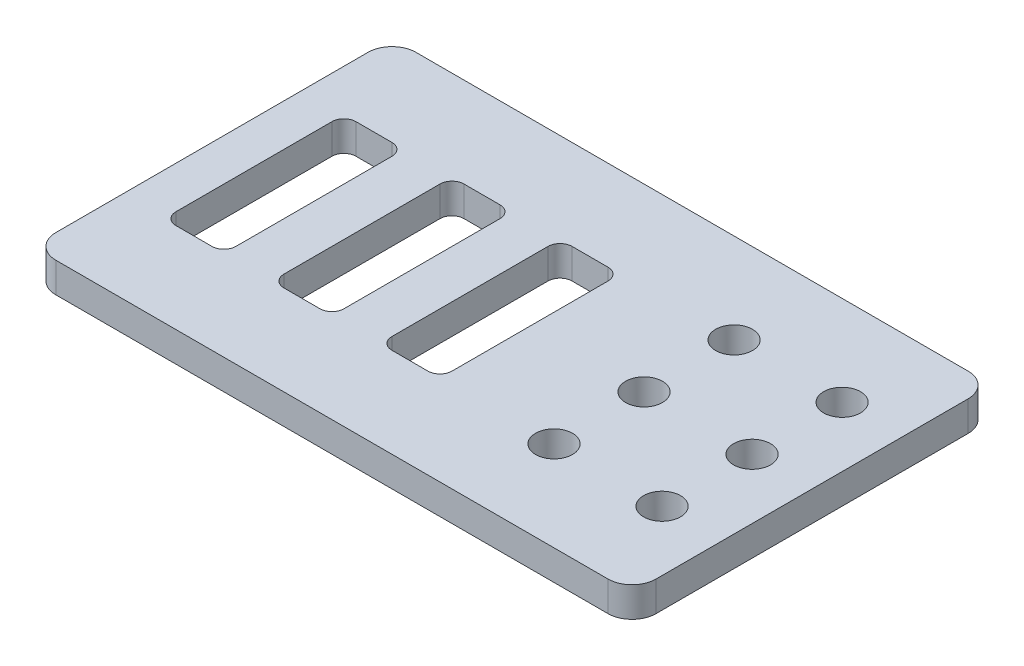
SolidWorks part; units mm, degrees
ref_plane "Front Plane" through (0, 0, 0) normal (0, 0, 1) x (1, 0, 0)
ref_plane "Top Plane" through (0, 0, 0) normal (0, 1, 0) x (1, 0, 0)
ref_plane "Right Plane" through (0, 0, 0) normal (1, 0, 0) x (0, 0, -1)
sketch "Sketch1" plane through (0, 0, 0) normal (0, 1, 0) x (1, 0, 0)
  line L1 (-50, -30) -> (50, -30)
  line L2 (-50, -30) -> (-50, 30)
  line L3 (-50, 30) -> (50, 30)
  line L4 (50, -30) -> (50, 30)
  line L5 (0, 30) -> (0, -30) construction
  line L6 (-50, 0) -> (50, 0) construction
  point P0 (0, 0)
  dimension "D1" = 60
  dimension "D2" = 100
extrude "Boss-Extrude1" add sketch "Sketch1" along normal blind 5
sketch "Sketch2" plane through (0, 5, 0) normal (0, 1, 0) x (1, 0, 0)
  line L0 (40, 30) -> (40, -30) construction
  line L1 (50, 30) -> (-50, 30) construction
  line L2 (-50, -30) -> (50, -30) construction
  line L3 (50, -30) -> (50, 30) construction
  circle A0 centre (40, 15) radius 3.075
  circle A1 centre (40, -15) radius 3.075
  circle A2 centre (40, 0) radius 3.075
  dimension "D1" = 6.15
  dimension "D3" = 15
  dimension "D4" = 15
  dimension "D2" = 10
extrude "Cut-Extrude1" cut sketch "Sketch2" against normal through all both and the other way through all
sketch "Sketch3" plane through (0, 5, 0) normal (0, 1, 0) x (1, 0, 0)
  line L0 (50, 0) -> (-50, 0) construction
  line L1 (50, -30) -> (50, 30) construction
  line L2 (-50, 30) -> (-50, -30) construction
  line L4 (-43, -15) -> (-33, -15)
  line L5 (-43, -15) -> (-43, 15)
  line L6 (-43, 15) -> (-33, 15)
  line L7 (-33, -15) -> (-33, 15)
  line L8 (-38, 15) -> (-38, -15) construction
  line L9 (-43, 0) -> (-33, 0) construction
  point P6 (-38, 0)
  dimension "D1" = 30
  dimension "D2" = 10
  dimension "D3" = 7
extrude "Cut-Extrude2" cut sketch "Sketch3" against normal through all
fillet "Fillet2" radius 2 4 edges at (-43, 2.5, 15) (-33, 2.5, -15) (-43, 2.5, -15) (-33, 2.5, 15)
pattern_linear "LPattern1" count 3 spacing 18 along (1, 0, 0) of "Cut-Extrude2", "Fillet2"
pattern_linear "LPattern2" count 2 spacing 18 along (-1, 0, 0) of "Cut-Extrude1"
fillet "Fillet1" radius 4 4 edges at (-50, 2.5, -30) (50, 2.5, -30) (50, 2.5, 30) (-50, 2.5, 30)
